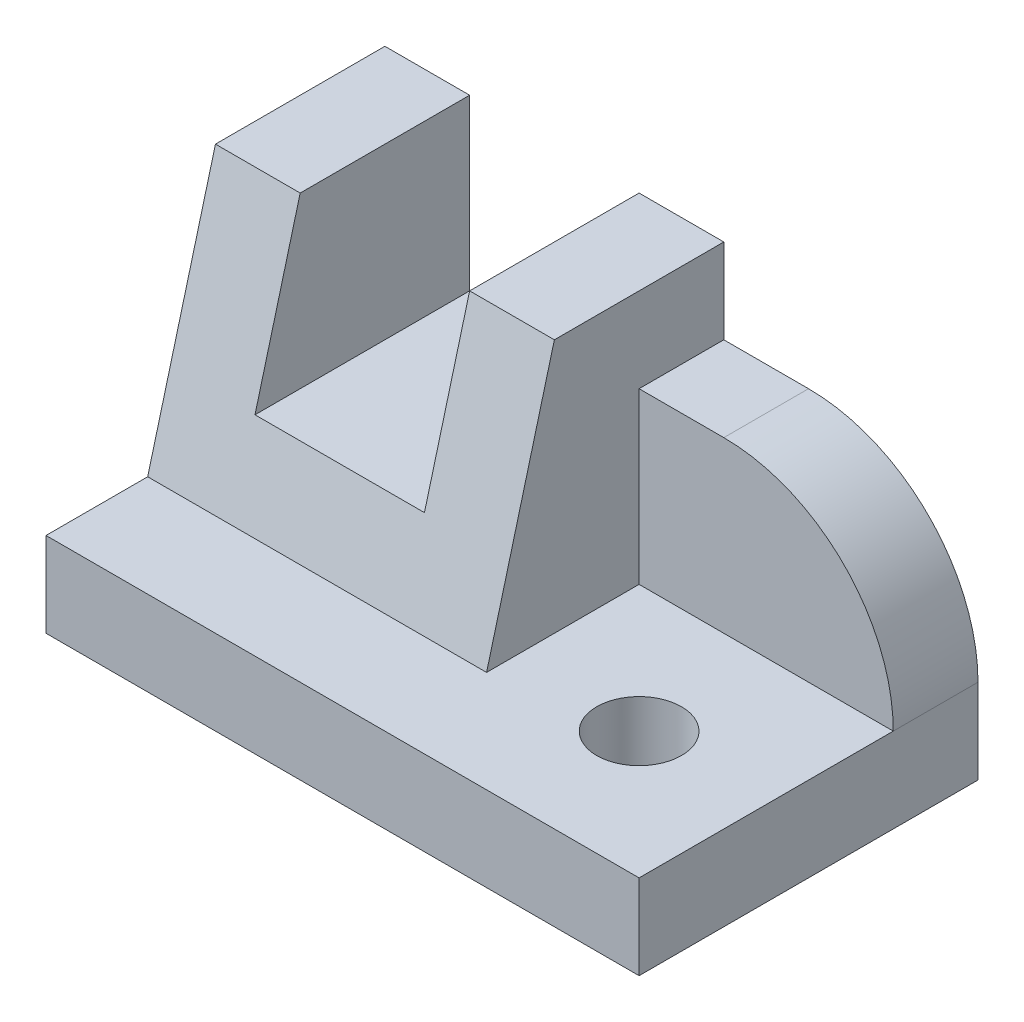
SolidWorks part; units mm, degrees
ref_plane "Front Plane" through (0, 0, 0) normal (0, 0, 1) x (1, 0, 0)
ref_plane "Top Plane" through (0, 0, 0) normal (0, 1, 0) x (1, 0, 0)
ref_plane "Right Plane" through (0, 0, 0) normal (1, 0, 0) x (0, 0, -1)
ref_plane "Plane1" through (0, 0, 0) normal (-1, 0, 0) x (0, -1, 0)
sketch "Sketch1" plane through (0, 0, 0) normal (-1, 0, 0) x (0, -1, 0)
  line L0 (-10, -12) -> (-40, -20)
  line L1 (-40, -20) -> (-10, -20)
  line L2 (-10, -20) -> (-10, -12)
  dimension "D1" = 30
  dimension "Width" = 8
extrude "Boss-Extrude1" add sketch "Sketch1" against normal blind 40
sketch "Sketch2" plane through (0, 0, -20) normal (0, 0, -1) x (-1, 0, 0)
  line L0 (-40, 40) -> (0, 40)
  line L1 (0, 40) -> (0, 10)
  line L2 (0, 10) -> (-40, 10)
  line L3 (-40, 10) -> (-40, 40)
extrude "Boss-Extrude2" add sketch "Sketch2" along normal blind 20
sketch "Sketch3" plane through (40, 0, 0) normal (1, 0, 0) x (0, 0, -1)
  line L0 (40, 10) -> (0, 10)
  line L1 (0, 10) -> (20, 40)
  line L2 (20, 40) -> (40, 40)
  line L3 (40, 40) -> (40, 10)
extrude "Boss-Extrude3" add sketch "Sketch3" along normal blind 30
sketch "Sketch4" plane through (70, 0, 0) normal (1, 0, 0) x (0, 0, -1)
  line L0 (20, 40) -> (0, 10)
  line L1 (0, 10) -> (30, 10)
  line L2 (30, 10) -> (30, 30)
  line L3 (30, 30) -> (40, 30)
  line L4 (40, 30) -> (40, 40)
  line L5 (40, 40) -> (20, 40)
extrude "Cut-Extrude1" cut sketch "Sketch4" against normal blind 30
sketch "Sketch5" plane through (0, 10, 0) normal (0, -1, 0) x (1, 0, 0)
  line L0 (70, 0) -> (70, -40)
  line L1 (70, -40) -> (0, -40)
  line L2 (0, -40) -> (0, 0)
  line L3 (0, 0) -> (70, 0)
extrude "Boss-Extrude4" add sketch "Sketch5" along normal blind 10
sketch "Sketch6" plane through (0, 0, -40) normal (0, 0, -1) x (-1, 0, 0)
  line L0 (-30, 40) -> (-30, 20)
  line L1 (-30, 20) -> (-10, 20)
  line L2 (-10, 20) -> (-10, 40)
  line L3 (-10, 40) -> (-30, 40)
extrude "Cut-Extrude2" cut sketch "Sketch6" against normal through all
hole_wizard "Ø10.0 (10) Diameter Hole1" positions "Sketch8" profile "Sketch7" hole size "Ø10.0" standard "ANSI Metric"
sketch "Sketch8" plane through (0, 0, 0) normal (0, -1, 0) x (-1, 0, 0)
  point P0 (-55, 15)
sketch "Sketch7" plane through (55, 0, -15) normal (1, 0, 0) x (0, 0, -1)
  line L0 (0, 0) -> (0, 40)
  line L1 (0, 40) -> (5, 40)
  line L2 (5, 40) -> (5, 0)
  line L5 (5, 0) -> (0, 0)
  line L11 (0, -6.35) -> (0, 107.95) construction
  dimension "Thru Hole Dia." = 10
  dimension "Thru Hole Depth" = 40
fillet "Fillet1" radius 20 1 edges at (70, 30, -35)
